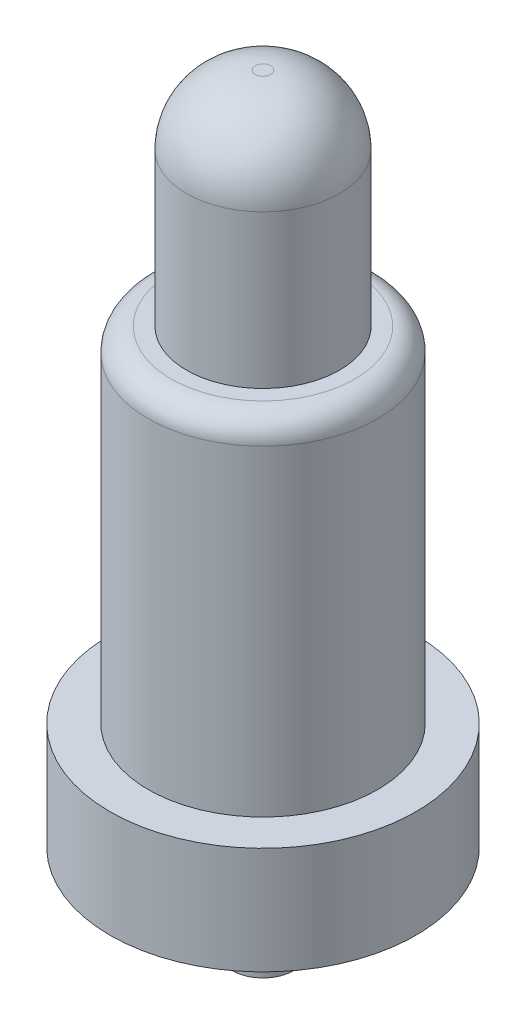
SolidWorks part; units mm, degrees
ref_plane "Front Plane" through (0, 0, 0) normal (0, 0, 1) x (1, 0, 0)
ref_plane "Top Plane" through (0, 0, 0) normal (0, 1, 0) x (1, 0, 0)
ref_plane "Right Plane" through (0, 0, 0) normal (1, 0, 0) x (0, 0, -1)
sketch "Sketch1" plane through (0, 0, 0) normal (0, 0, 1) x (1, 0, 0)
  line L0 (0, 0) -> (0, 5) construction
  line L1 (0, 0) -> (-0.2, 0)
  line L2 (-0.2, 0) -> (-0.2, 0.6)
  line L3 (-0.2, 0.6) -> (-1, 0.6)
  line L4 (-1, 0.6) -> (-1, 1.3)
  line L5 (-1, 1.3) -> (-0.75, 1.3)
  line L6 (-0.75, 1.3) -> (-0.75, 3.4)
  line L7 (-0.6, 3.55) -> (-0.5, 3.55)
  line L8 (-0.5, 3.55) -> (-0.5, 4.55)
  line L9 (-0.05, 5) -> (0, 5)
  line L10 (0, 0) -> (0, 5)
  arc A0 (-0.75, 3.4) -> (-0.6, 3.55) centre (-0.6, 3.4) cw
  arc A1 (-0.5, 4.55) -> (-0.05, 5) centre (-0.05, 4.55) cw
  point P7 (-0.6, 0.6)
  dimension "D9" = 0.15
  dimension "D10" = 0.45
  dimension "D1" = 5
  dimension "D2" = 0.4
  dimension "D3" = 0.6
  dimension "D4" = 2
  dimension "D5" = 0.7
  dimension "D6" = 1.5
  dimension "D7" = 1
  dimension "D8" = 2.95
revolve "Revolve1" add sketch "Sketch1" angle 360 about L0
